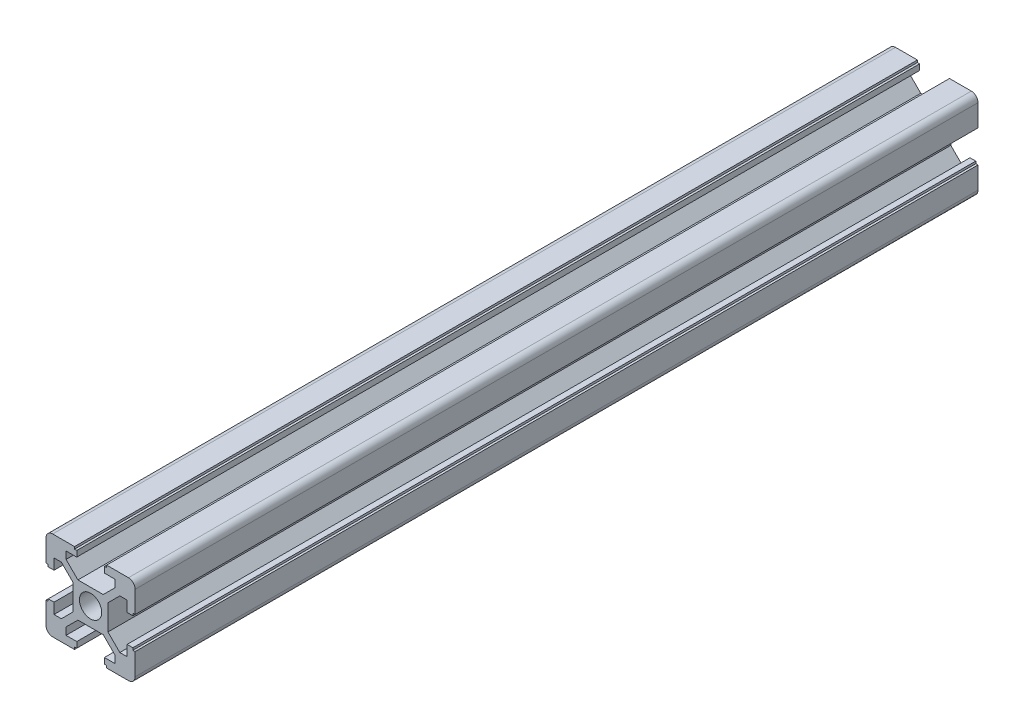
SolidWorks part; units mm, degrees
ref_plane "Front Plane" through (0, 0, 0) normal (0, 0, 1) x (1, 0, 0)
ref_plane "Top Plane" through (0, 0, 0) normal (0, 1, 0) x (1, 0, 0)
ref_plane "Right Plane" through (0, 0, 0) normal (1, 0, 0) x (0, 0, -1)
sketch "Sketch1" plane through (0, 0, 0) normal (0, 0, 1) x (1, 0, 0)
  line L0 (0, 13.3843) -> (0, -12.9126) construction
  line L1 (-14.4653, 0) -> (14.4653, 0) construction
  line L2 (2.8393, 3.9) -> (5.5, 6.5607)
  line L3 (-8.5, 10) -> (-3.6, 10)
  line L4 (-10, 8.5) -> (-10, 3.6)
  line L5 (-8.5, -10) -> (-3.6, -10)
  line L6 (10, 8.5) -> (10, 3.6)
  line L7 (-10, 10) -> (10, -10) construction
  line L8 (-10, -10) -> (10, 10) construction
  line L9 (-5.5, 8.2) -> (-3.1, 8.2)
  line L10 (-5.9626, 4.902) -> (-4.902, 5.9626) construction
  line L11 (-2.8393, 3.9) -> (-5.5, 6.5607)
  line L12 (-5.5, 8.2) -> (-5.5, 6.5607)
  line L13 (-2.8393, 3.9) -> (2.8393, 3.9)
  line L14 (5.5, 8.2) -> (5.5, 6.5607)
  line L15 (-3.1, 9.5) -> (-3.1, 8.2)
  line L16 (3.1, 9.5) -> (3.1, 8.2)
  line L17 (-3.1, 9.5) -> (3.1, 9.5) construction
  line L18 (-3.1, 9.5) -> (-3.6, 9.5)
  line L19 (-3.6, 9.5) -> (-3.6, 10)
  line L20 (3.1, 9.5) -> (3.6, 9.5)
  line L21 (3.6, 9.5) -> (3.6, 10)
  line L22 (3.6, 10) -> (8.5, 10)
  line L23 (3.1, 8.2) -> (5.5, 8.2)
  line L24 (-9.5, -3.1) -> (-9.5, -3.6)
  line L25 (-9.5, -3.6) -> (-10, -3.6)
  line L26 (-9.5, -3.1) -> (-8.2, -3.1)
  line L27 (-8.2, -3.1) -> (-8.2, -5.5)
  line L28 (-8.2, -5.5) -> (-6.5607, -5.5)
  line L29 (-3.9, -2.8393) -> (-6.5607, -5.5)
  line L30 (-3.9, 2.8393) -> (-3.9, -2.8393)
  line L31 (-3.9, 2.8393) -> (-6.5607, 5.5)
  line L32 (-8.2, 5.5) -> (-6.5607, 5.5)
  line L33 (-8.2, 5.5) -> (-8.2, 3.1)
  line L34 (-9.5, 3.1) -> (-8.2, 3.1)
  line L35 (-9.5, 3.1) -> (-9.5, 3.6)
  line L36 (-9.5, 3.6) -> (-10, 3.6)
  line L37 (-3.6, -9.5) -> (-3.6, -10)
  line L38 (-3.1, -9.5) -> (-3.6, -9.5)
  line L39 (-3.1, -9.5) -> (-3.1, -8.2)
  line L40 (-3.1, -8.2) -> (-5.5, -8.2)
  line L41 (-5.5, -8.2) -> (-5.5, -6.5607)
  line L42 (-2.8393, -3.9) -> (-5.5, -6.5607)
  line L43 (2.8393, -3.9) -> (-2.8393, -3.9)
  line L44 (2.8393, -3.9) -> (5.5, -6.5607)
  line L45 (5.5, -8.2) -> (5.5, -6.5607)
  line L46 (5.5, -8.2) -> (3.1, -8.2)
  line L47 (3.1, -9.5) -> (3.6, -9.5)
  line L48 (3.1, -9.5) -> (3.1, -8.2)
  line L49 (3.6, -9.5) -> (3.6, -10)
  line L50 (9.5, -3.6) -> (10, -3.6)
  line L51 (9.5, -3.1) -> (9.5, -3.6)
  line L52 (9.5, -3.1) -> (8.2, -3.1)
  line L53 (8.2, -5.5) -> (8.2, -3.1)
  line L54 (8.2, -5.5) -> (6.5607, -5.5)
  line L55 (3.9, -2.8393) -> (6.5607, -5.5)
  line L56 (3.9, -2.8393) -> (3.9, 2.8393)
  line L57 (3.9, 2.8393) -> (6.5607, 5.5)
  line L58 (8.2, 5.5) -> (6.5607, 5.5)
  line L59 (8.2, 3.1) -> (8.2, 5.5)
  line L60 (9.5, 3.1) -> (8.2, 3.1)
  line L61 (9.5, 3.1) -> (9.5, 3.6)
  line L62 (9.5, 3.6) -> (10, 3.6)
  line L63 (-10, -3.6) -> (-10, -8.5)
  line L64 (3.6, -10) -> (8.5, -10)
  line L65 (10, -3.6) -> (10, -8.5)
  arc A0 (8.5, 10) -> (10, 8.5) centre (8.5, 8.5) cw
  arc A1 (8.5, -10) -> (10, -8.5) centre (8.5, -8.5) ccw
  arc A2 (-10, -8.5) -> (-8.5, -10) centre (-8.5, -8.5) ccw
  arc A3 (-8.5, 10) -> (-10, 8.5) centre (-8.5, 8.5) ccw
  circle A4 centre (0, 0.2358) radius 2.5
  point P5 (0, 0)
  point P30 (-5.4323, 5.4323)
  point P38 (0, 9.5)
  dimension "D3" = 1.5
  dimension "D15" = 5
  dimension "D1" = 20
  dimension "D2" = 20
  dimension "D4" = 6.2
  dimension "D5" = 11
  dimension "D6" = 1.8
  dimension "D7" = 1.5
  dimension "D8" = 90
  dimension "D9" = 0.5
  dimension "D10" = 0.5
  dimension "D11" = 0.5
  dimension "D12" = 0.5
  dimension "D13" = 6.1
  dimension "D14" = 45
extrude "Boss-Extrude1" add sketch "Sketch1" along normal blind 189.0961
scale "缩放比例1" bodies to scale 101 scale about centroid uniform scaling yes scale factor 1
scale "缩放比例2" scale about centroid uniform scaling yes scale factor 3
scale "缩放比例3" scale about centroid uniform scaling yes scale factor 6
scale "缩放比例5" scale about centroid uniform scaling yes scale factor 2
scale "缩放比例6" scale about centroid uniform scaling yes scale factor 0.25
scale "缩放比例7" scale about centroid uniform scaling yes scale factor 0.125
scale "缩放比例8" scale about centroid uniform scaling yes scale factor 0.25
scale "缩放比例9" scale about centroid uniform scaling yes scale factor 4
scale "缩放比例10" scale about centroid uniform scaling yes scale factor 4
sketch "草图5" plane through (0, -44.9052, 0) normal (0, -1, 0) x (-1, 0, 0)
  circle A0 centre (26.2054, 311.8546) radius 5.1526
scale "缩放比例11" scale about centroid uniform scaling yes scale factor 0.111111
